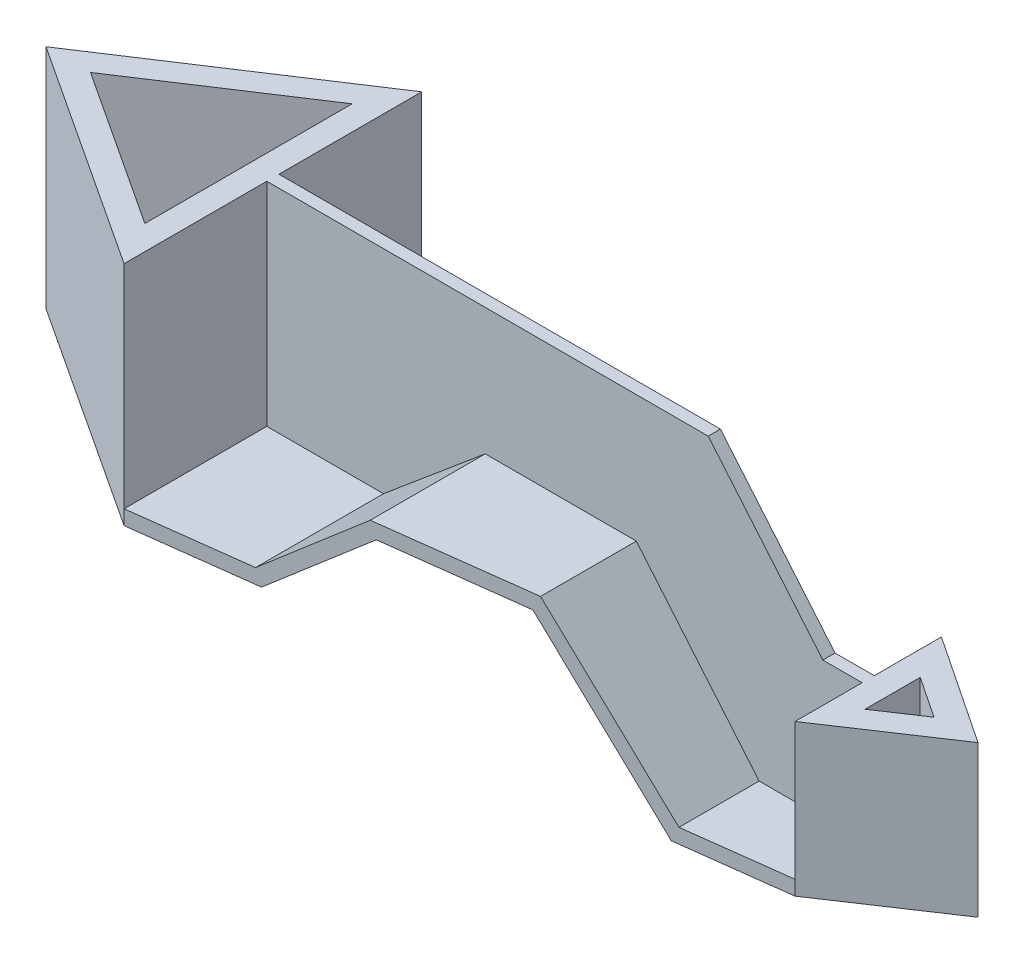
SolidWorks part; units mm, degrees
material "1060 Alloy"
ref_plane "Front Plane" through (0, 0, 0) normal (0, 0, 1) x (1, 0, 0)
ref_plane "Top Plane" through (0, 0, 0) normal (0, 1, 0) x (1, 0, 0)
ref_plane "Right Plane" through (0, 0, 0) normal (1, 0, 0) x (0, 0, -1)
sketch "Sketch2" plane through (0, 0, 0) normal (0, 1, 0) x (1, 0, 0)
  line L0 (0, -61) -> (0, 61)
  line L1 (0, 61) -> (-93, 0)
  line L2 (-93, 0) -> (0, -61)
  line L3 (-10, 42.4817) -> (-74.7671, 0)
  line L4 (-74.7671, 0) -> (-10, -42.4817)
  line L5 (-10, -42.4817) -> (-10, 42.4817)
  point P0 (0, 0)
  point P4 (0, 0)
  dimension "D1" = 61
  dimension "D2" = 93
  dimension "D3" = 10
extrude "Boss-Extrude1" add sketch "Sketch2" along normal blind 93
sketch "Sketch3" plane through (0, 0, 0) normal (0, 0, 1) x (1, 0, 0)
  line L0 (0, 0) -> (50, 0)
  line L1 (50, 0) -> (91.7114, 35)
  line L2 (91.7114, 35) -> (148.654, 35)
  line L3 (148.654, 35) -> (199, -25)
  line L4 (199, -25) -> (244, -25)
  line L5 (0, 6) -> (47.8162, 6)
  line L6 (47.8162, 6) -> (89.5276, 41)
  line L7 (89.5276, 41) -> (151.4519, 41)
  line L8 (151.4519, 41) -> (201.7978, -19)
  line L9 (201.7978, -19) -> (244, -19)
  line L10 (0, 6) -> (0, 0)
  line L11 (244, -19) -> (244, -25)
  dimension "D1" = 50
  dimension "D2" = 35
  dimension "D3" = 60
  dimension "D4" = 45
  dimension "D5" = 140
  dimension "D6" = 130
  dimension "D7" = 244
  dimension "D8" = 6
extrude "Boss-Extrude2" add sketch "Sketch3" along normal mid plane 122
sketch "Sketch4" plane through (0, 0, 0) normal (0, 1, 0) x (1, 0, 0)
  line L0 (244, -30) -> (244, 30)
  line L1 (244, -61) -> (244, 61) construction
  line L2 (244, 30) -> (289, 0)
  line L3 (289, 0) -> (244, -30)
  line L4 (254, 11.3148) -> (270.9722, 0)
  line L5 (270.9722, 0) -> (254, -11.3148)
  line L6 (254, -11.3148) -> (254, 11.3148)
  point P5 (244, 0)
  point P6 (0, 0)
  point P7 (0, 0)
  point P9 (275.0804, 0)
  dimension "D1" = 30
  dimension "D2" = 45
  dimension "D3" = 10
extrude "Boss-Extrude3" add sketch "Sketch4" along normal blind 62 from surface at -25 starting at face at (221.5, -25, 0)
sketch "Sketch7" plane through (0, 0, 0) normal (0, 0, 1) x (1, 0, 0)
  line L0 (0, 93) -> (180.9215, 93)
  line L1 (180.9215, 93) -> (227.9111, 37)
  line L2 (227.9111, 37) -> (244, 37)
  line L3 (148.654, 35) -> (199, -25) construction
  line L4 (0, 93) -> (0, 6)
  line L5 (0, 6) -> (47.8162, 6)
  line L6 (47.8162, 6) -> (89.5276, 41)
  line L7 (89.5276, 41) -> (151.4519, 41)
  line L8 (151.4519, 41) -> (201.7978, -19)
  line L9 (201.7978, -19) -> (244, -19)
  line L10 (244, -19) -> (244, 37)
  dimension "D1" = 62
extrude "Boss-Extrude4" add sketch "Sketch7" along normal mid plane 5
sketch "Sketch8" plane through (0, 0, 0) normal (0, 1, 0) x (1, 0, 0)
  line L0 (0, 61) -> (244, 61)
  line L1 (244, 61) -> (244, 30)
  line L2 (244, 30) -> (0, 61)
  line L3 (0, -61) -> (244, -30)
  line L4 (244, -30) -> (244, -61)
  line L5 (244, -61) -> (0, -61)
extrude "Cut-Extrude2" cut sketch "Sketch8" against normal through all both and the other way through all
equation "\"A\" = 244"
equation "\"B\"= 93"
equation "\"D1@Sketch2\"=\"A\"/4"
equation "\"D2@Sketch2\"=\"B\""
equation "\"D1@Boss-Extrude1\"=\"B\""
equation "\"D7@Sketch3\"=\"A\""
equation "\"D1@Boss-Extrude2\"=\"A\"/2"
equation "\"D1@Boss-Extrude3\"=\"B\"*2/3"
equation "\"D1@Sketch7\"=\"B\"*2/3"
equation "\"D1@Boss-Extrude4\"=\"A\"/2"
